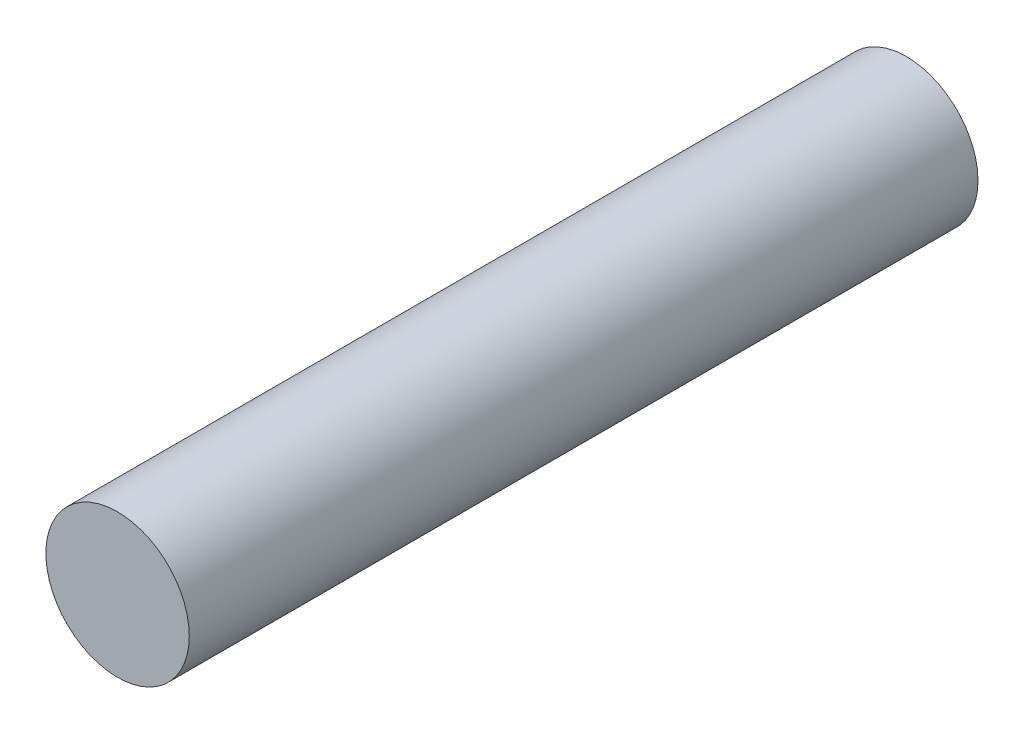
SolidWorks part; units mm, degrees
ref_plane "Front Plane" through (0, 0, 0) normal (0, 0, 1) x (1, 0, 0)
ref_plane "Top Plane" through (0, 0, 0) normal (0, 1, 0) x (1, 0, 0)
ref_plane "Right Plane" through (0, 0, 0) normal (1, 0, 0) x (0, 0, -1)
sketch "Sketch1" plane through (0, 0, 0) normal (0, 0, 1) x (1, 0, 0)
  circle A0 centre (0, 0) radius 3.175
extrude "Boss-Extrude1" add sketch "Sketch1" along normal blind 34.925
